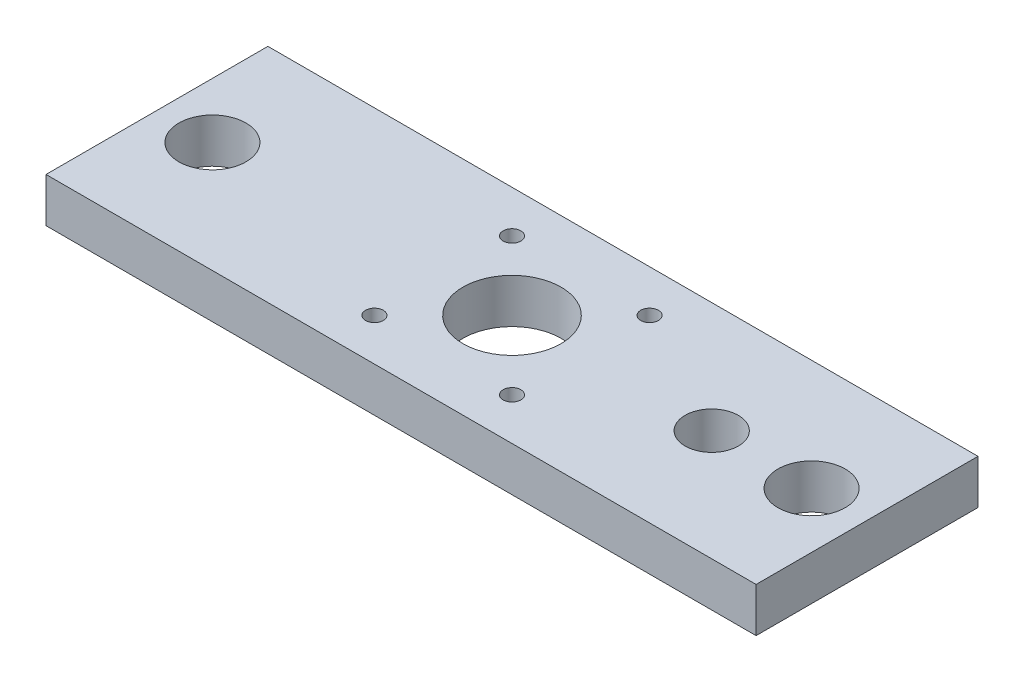
SolidWorks part; units mm, degrees
ref_plane "Front Plane" through (0, 0, 0) normal (0, 0, 1) x (1, 0, 0)
ref_plane "Top Plane" through (0, 0, 0) normal (0, 1, 0) x (1, 0, 0)
ref_plane "Right Plane" through (0, 0, 0) normal (1, 0, 0) x (0, 0, -1)
sketch "Sketch1" plane through (0, 0, 0) normal (0, 1, 0) x (1, 0, 0)
  line L0 (-67.5, 0) -> (67.5, 0) construction
  line L1 (-80, -25) -> (80, -25)
  line L2 (-80, -25) -> (-80, 25)
  line L3 (-80, 25) -> (80, 25)
  line L4 (80, -25) -> (80, 25)
  line L5 (-80, -25) -> (80, 25) construction
  line L6 (-80, 25) -> (80, -25) construction
  line L7 (-15.5, -15.5) -> (15.5, -15.5) construction
  line L8 (-15.5, -15.5) -> (-15.5, 15.5) construction
  line L9 (-15.5, 15.5) -> (15.5, 15.5) construction
  line L10 (15.5, -15.5) -> (15.5, 15.5) construction
  line L11 (-15.5, -15.5) -> (15.5, 15.5) construction
  line L12 (-15.5, 15.5) -> (15.5, -15.5) construction
  circle A0 centre (0, 0) radius 11.05
  circle A1 centre (15.5, 15.5) radius 2
  circle A2 centre (-15.5, 15.5) radius 2
  circle A3 centre (-15.5, -15.5) radius 2
  circle A4 centre (15.5, -15.5) radius 2
  circle A5 centre (-67.5, 0) radius 7.575
  circle A6 centre (67.5, 0) radius 7.575
  circle A7 centre (45, 0) radius 6
  point P0 (0, 0)
  point P21 (0, 0)
  dimension "D3" = 22.1
  dimension "D5" = 4
  dimension "D7" = 15.15
  dimension "D8" = 125
  dimension "D9" = 12
  dimension "D1" = 160
  dimension "D2" = 50
  dimension "D4" = 31
  dimension "D6" = 135
extrude "Boss-Extrude1" add sketch "Sketch1" along normal blind 10
